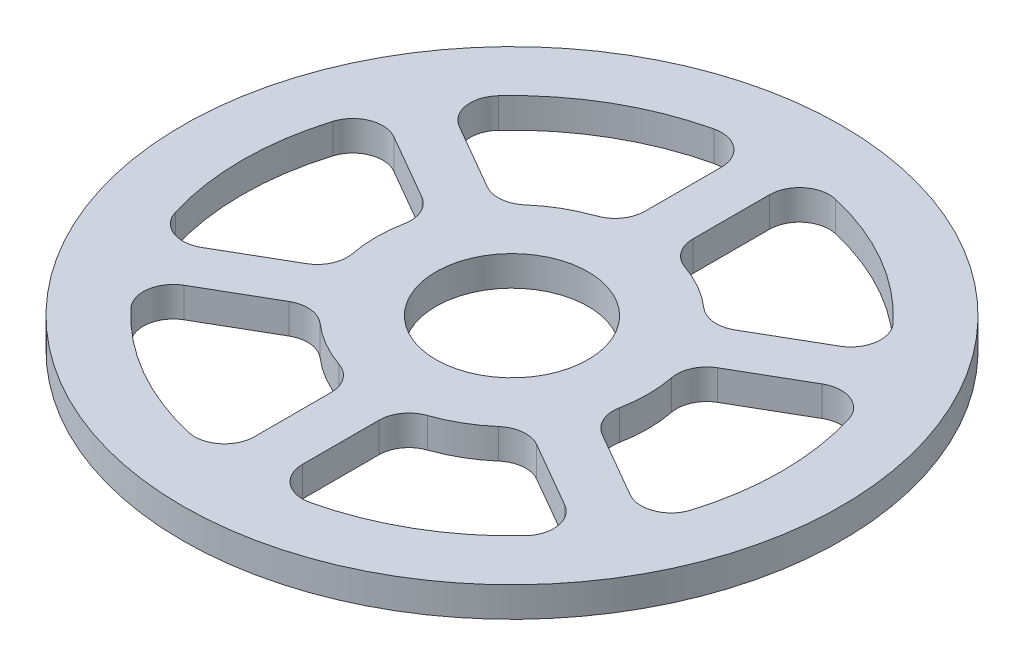
SolidWorks part; units mm, degrees
material "ABS"
ref_plane "Front Plane" through (0, 0, 0) normal (0, 0, 1) x (1, 0, 0)
ref_plane "Top Plane" through (0, 0, 0) normal (0, 1, 0) x (1, 0, 0)
ref_plane "Right Plane" through (0, 0, 0) normal (1, 0, 0) x (0, 0, -1)
sketch "Sketch1" plane through (0, 0, 0) normal (0, 1, 0) x (1, 0, 0)
  circle A0 centre (0, 0) radius 55
  dimension "D1" = 110
extrude "Boss-Extrude1" add sketch "Sketch1" along normal blind 5
sketch "Sketch2" plane through (0, 0, 0) normal (0, 1, 0) x (1, 0, 0)
  circle A0 centre (0, 0) radius 51 construction
  circle A1 centre (0, 51) radius 1.5
  circle A2 centre (44.1673, 25.5) radius 1.5
  circle A3 centre (44.1673, -25.5) radius 1.5
  circle A4 centre (0, -51) radius 1.5
  circle A5 centre (-44.1673, -25.5) radius 1.5
  circle A6 centre (-44.1673, 25.5) radius 1.5
  point P17 (0, 0)
  dimension "D1" = 102
  dimension "D2" = 3
  dimension "D3" = 6
extrude "Cut-Extrude1" cut sketch "Sketch2" along normal blind 2.5
sketch "Sketch5" plane through (0, 5, 0) normal (0, 1, 0) x (1, 0, 0)
  circle A0 centre (0, 0) radius 12.7
  dimension "D1" = 25.4
extrude "Cut-Extrude4" cut sketch "Sketch5" against normal through all
sketch "Sketch7" plane through (0, 5, 0) normal (0, 1, 0) x (1, 0, 0)
  line L0 (0, 45) -> (0, 0) construction
  line L1 (-4, 45) -> (-4, 22.3448)
  line L2 (4, 45) -> (4, 22.3448)
  line L3 (36.9711, 25.9641) -> (17.3512, 14.6365)
  line L4 (-4, 45) -> (-4, 0) construction
  line L5 (40.9711, 19.0359) -> (21.3512, 7.7083)
  line L6 (4, 45) -> (4, 0) construction
  line L7 (40.9711, -19.0359) -> (21.3512, -7.7083)
  line L8 (36.9711, -25.9641) -> (17.3512, -14.6365)
  line L9 (4, -45) -> (4, -22.3448)
  line L10 (-4, -45) -> (-4, -22.3448)
  line L11 (-36.9711, -25.9641) -> (-17.3512, -14.6365)
  line L12 (-40.9711, -19.0359) -> (-21.3512, -7.7083)
  line L13 (-40.9711, 19.0359) -> (-21.3512, 7.7083)
  line L14 (-36.9711, 25.9641) -> (-17.3512, 14.6365)
  circle A1 centre (0, 0) radius 22.7
  circle A2 centre (0, 0) radius 45
  circle A6 centre (0, 0) radius 12.7 construction
  circle A7 centre (0, 0) radius 55
  circle A8 centre (0, 0) radius 55
  circle A9 centre (0, 0) radius 12.7
  point P37 (0, 0)
  dimension "D1" = 0
  dimension "D2" = 10
  dimension "D3" = 10
  dimension "D4" = 4
  dimension "D5" = 4
  dimension "D6" = 6
extrude "Cut-Extrude5" cut sketch "Sketch7" against normal through all contours L13 A2 L12 A1 | L11 A2 L10 A1 | L9 A2 L8 A1 | L7 A2 L5 A1 | L3 A2 L2 A1 | L1 A2 L14 A1
fillet "Fillet1" radius 5 4 edges at (-21.3512, 2.5, 7.7083) (-21.3512, 2.5, -7.7083) (-40.8169, 2.5, 18.9468) (-40.8169, 2.5, -18.9468)
fillet "Fillet2" radius 5 20 edges at (-4, 2.5, 44.8219) (-4, 2.5, 22.3448) (-17.3512, 2.5, 14.6365) (-36.8169, 2.5, 25.875) (36.8169, 2.5, 25.875) (4, 2.5, 44.8219) (4, 2.5, 22.3448) (17.3512, 2.5, 14.6365) (40.8169, 2.5, 18.9468) (21.3512, 2.5, 7.7083) (21.3512, 2.5, -7.7083) (40.8169, 2.5, -18.9468) (36.8169, 2.5, -25.875) (4, 2.5, -44.8219) (17.3512, 2.5, -14.6365) (4, 2.5, -22.3448) (-4, 2.5, -22.3448) (-17.3512, 2.5, -14.6365) (-36.8169, 2.5, -25.875) (-4, 2.5, -44.8219)
